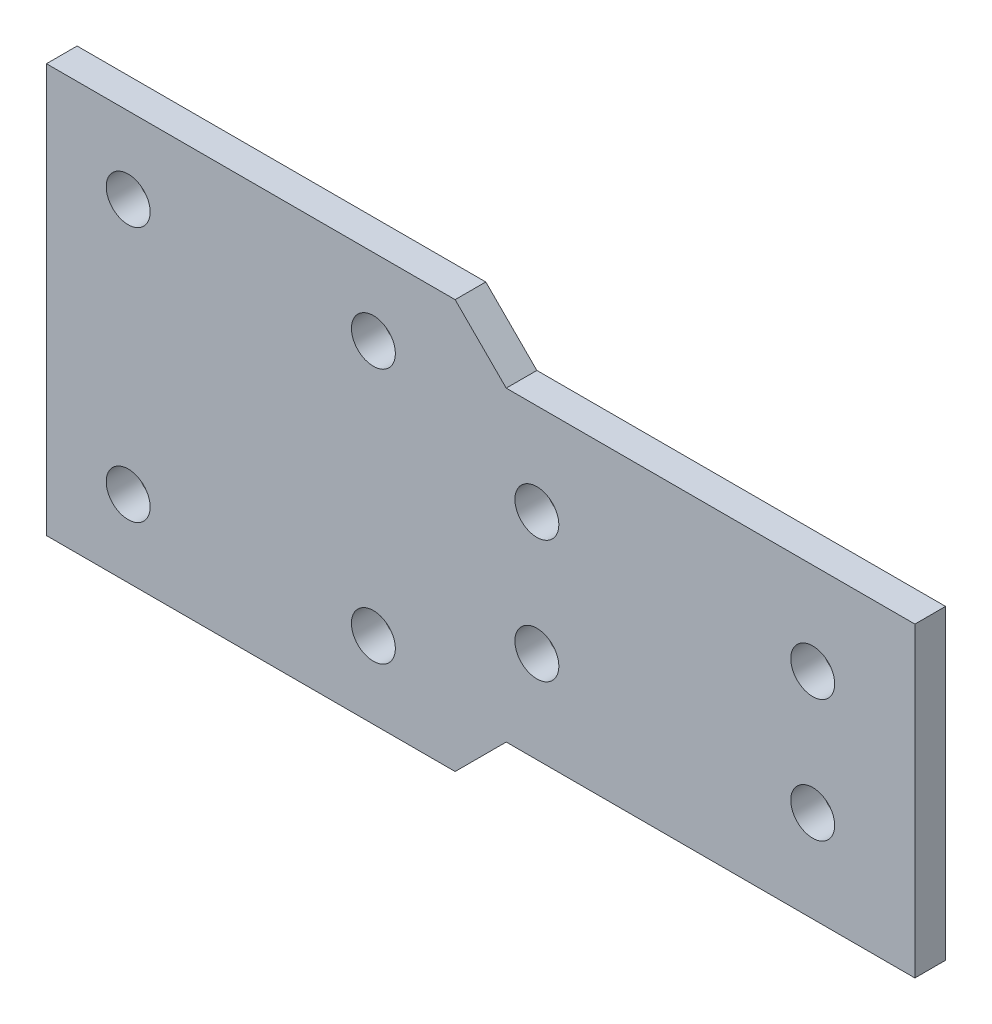
SolidWorks part; units mm, degrees
material "Thornel Mat VMA"
ref_plane "Front Plane" through (0, 0, 0) normal (0, 0, 1) x (1, 0, 0)
ref_plane "Top Plane" through (0, 0, 0) normal (0, 1, 0) x (1, 0, 0)
ref_plane "Right Plane" through (0, 0, 0) normal (1, 0, 0) x (0, 0, -1)
sketch "Sketch1" plane through (0, 0, 0) normal (0, 0, 1) x (1, 0, 0)
  line L0 (0, 20) -> (5, 15)
  line L1 (-40, 20) -> (0, 20)
  line L2 (-40, 20) -> (-40, -20)
  line L3 (-40, -20) -> (0, -20)
  line L5 (5, 15) -> (45, 15)
  line L7 (5, -15) -> (45, -15)
  line L8 (45, 15) -> (45, -15)
  line L9 (5, -15) -> (0, -20)
  line L10 (-300, 17) -> (0, 17) construction
  line L12 (-300, 12.5) -> (-34.15, 12.5) construction
  line L13 (-32, 12.5) -> (-8, 12.5) construction
  line L14 (-32, 12.5) -> (-32, -12.5) construction
  line L15 (-32, -12.5) -> (-8, -12.5) construction
  line L16 (-8, 12.5) -> (-8, -12.5) construction
  line L17 (-300, -12.5) -> (-34.15, -12.5) construction
  line L18 (0, -5) -> (0, 5) construction
  line L19 (45, 10) -> (0, 10) construction
  line L20 (45, 10) -> (45, -10) construction
  line L21 (45, -10) -> (0, -10) construction
  line L22 (0, 10) -> (0, -10) construction
  line L23 (8, 6) -> (35, 6) construction
  line L24 (8, 6) -> (8, -6) construction
  line L25 (8, -6) -> (35, -6) construction
  line L26 (35, 6) -> (35, -6) construction
  line L27 (0, 5) -> (0, 16.5) construction
  circle A0 centre (-32, 12.5) radius 2.15
  circle A1 centre (-8, 12.5) radius 2.15
  circle A2 centre (-32, -12.5) radius 2.15
  circle A3 centre (-8, -12.5) radius 2.15
  circle A4 centre (8, 6) radius 2.15
  circle A5 centre (8, -6) radius 2.15
  circle A6 centre (35, 6) radius 2.15
  circle A7 centre (35, -6) radius 2.15
  dimension "D10" = 4.3
  dimension "D17" = 4.3
  dimension "D1" = 40
  dimension "D2" = 3
  dimension "D3" = 30
  dimension "D4" = 135
  dimension "D5" = 135
  dimension "D6" = 40
  dimension "D7" = 40
  dimension "D8" = 8
  dimension "D9" = 20
  dimension "D11" = 5
  dimension "D12" = 4
  dimension "D13" = 4
  dimension "D14" = 8
  dimension "D15" = 10
  dimension "D16" = 5
extrude "Extrude1" add sketch "Sketch1" along normal blind 3
